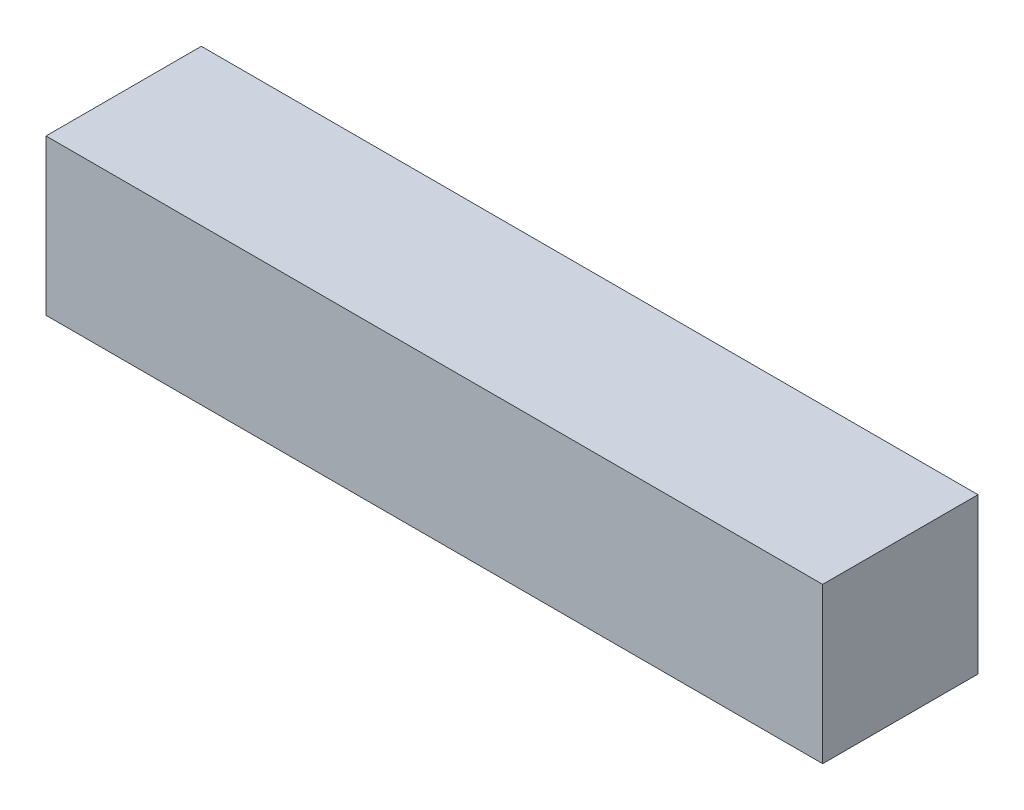
SolidWorks part; units mm, degrees
ref_plane "Front Plane" through (0, 0, 0) normal (0, 0, 1) x (1, 0, 0)
ref_plane "Top Plane" through (0, 0, 0) normal (0, 1, 0) x (1, 0, 0)
ref_plane "Right Plane" through (0, 0, 0) normal (1, 0, 0) x (0, 0, -1)
sketch "Sketch2" plane through (0, 0, 0) normal (0, 0, 1) x (1, 0, 0)
  line L0 (0, 0) -> (100, 0)
  line L1 (100, 0) -> (100, 20)
  line L2 (100, 20) -> (0, 20)
  line L3 (0, 20) -> (0, 0)
  dimension "D1" = 100
  dimension "D2" = 20
extrude "Boss-Extrude1" add sketch "Sketch2" along normal blind 20
